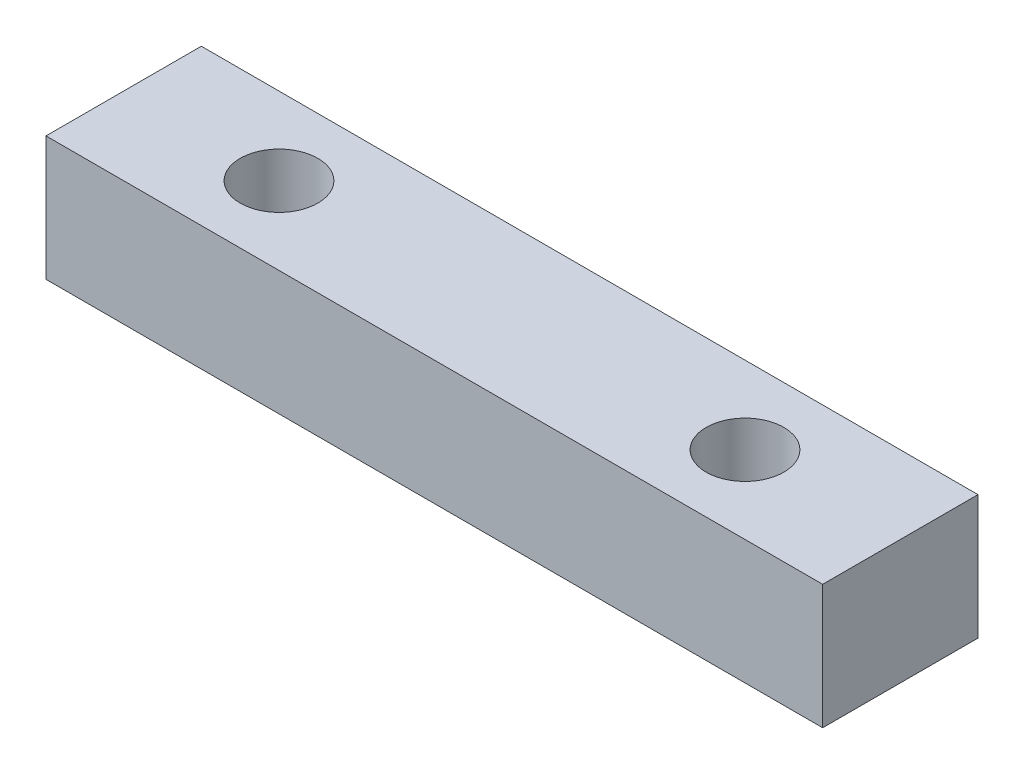
SolidWorks part; units mm, degrees
ref_plane "정면" through (0, 0, 0) normal (0, 0, 1) x (1, 0, 0)
ref_plane "윗면" through (0, 0, 0) normal (0, 1, 0) x (1, 0, 0)
ref_plane "우측면" through (0, 0, 0) normal (1, 0, 0) x (0, 0, -1)
sketch "스케치1" plane through (0, 0, 0) normal (0, 1, 0) x (1, 0, 0)
  line L0 (12.5, 2.5) -> (-12.5, 2.5)
  line L1 (12.5, 2.5) -> (-12.5, 2.5) construction
  line L2 (12.5, 2.5) -> (12.5, -2.5)
  line L3 (12.5, -2.5) -> (-12.5, -2.5)
  line L4 (-12.5, 2.5) -> (-12.5, -2.5)
  circle A1 centre (7.5, 0) radius 1.25
  circle A2 centre (-7.5, 0) radius 1.25
  point P4 (0, 2.5)
  point P6 (12.5, 0)
  dimension "D3" = 7.5
  dimension "D1" = 2.5
  dimension "D2" = 7.5
  dimension "D4" = 25
  dimension "D5" = 5
extrude "보스-돌출1" add sketch "스케치1" along normal blind 4
